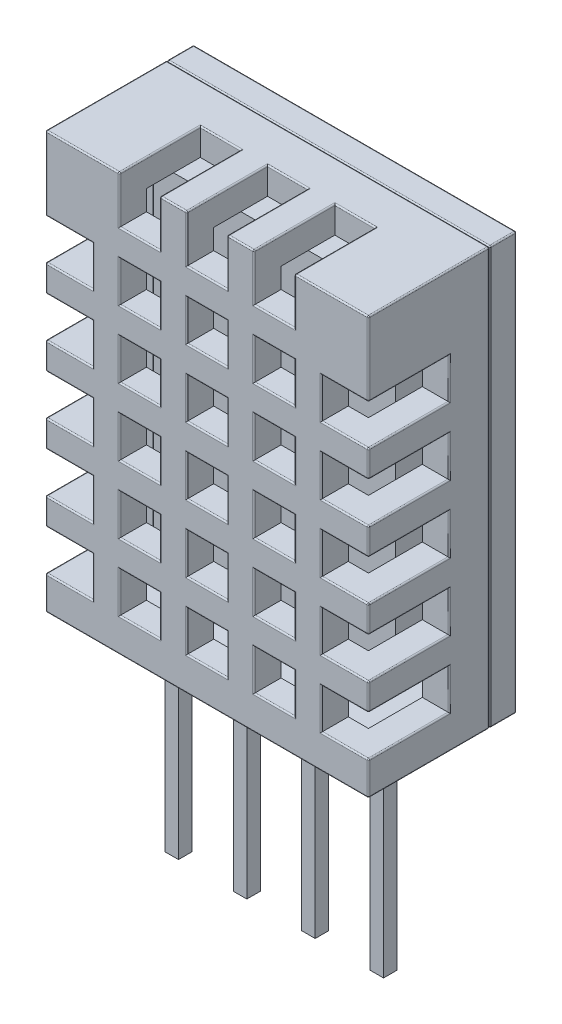
SolidWorks part; units mm, degrees
ref_plane "Front Plane" through (0, 0, 0) normal (0, 0, 1) x (1, 0, 0)
ref_plane "Top Plane" through (0, 0, 0) normal (0, 1, 0) x (1, 0, 0)
ref_plane "Right Plane" through (0, 0, 0) normal (1, 0, 0) x (0, 0, -1)
sketch "Sketch1" plane through (0, 0, 0) normal (0, 0, 1) x (1, 0, 0)
  line L1 (0, 0) -> (12, 0)
  line L2 (0, 0) -> (0, 15.5)
  line L3 (0, 15.5) -> (12, 15.5)
  line L4 (12, 0) -> (12, 15.5)
  dimension "D1" = 12
  dimension "D2" = 15.5
extrude "Boss-Extrude1" add sketch "Sketch1" along normal blind 5.5
sketch "Sketch2" plane through (0, 0, 0) normal (0, -1, 0) x (1, 0, 0)
  line L0 (0, 5.5) -> (0, 0) construction
  line L1 (1.94, 3) -> (2.44, 3)
  line L2 (1.94, 3) -> (1.94, 2.5)
  line L3 (1.94, 2.5) -> (2.44, 2.5)
  line L4 (2.44, 3) -> (2.44, 2.5)
  line L5 (0, 2.75) -> (12, 2.75) construction
  line L6 (12, 5.5) -> (12, 0) construction
  line L7 (4.48, 3) -> (4.98, 3)
  line L8 (4.48, 3) -> (4.48, 2.5)
  line L9 (4.48, 2.5) -> (4.98, 2.5)
  line L10 (4.98, 3) -> (4.98, 2.5)
  line L11 (7.02, 3) -> (7.52, 3)
  line L12 (7.02, 3) -> (7.02, 2.5)
  line L13 (7.02, 2.5) -> (7.52, 2.5)
  line L14 (7.52, 3) -> (7.52, 2.5)
  line L15 (9.56, 3) -> (10.06, 3)
  line L16 (9.56, 3) -> (9.56, 2.5)
  line L17 (9.56, 2.5) -> (10.06, 2.5)
  line L18 (10.06, 3) -> (10.06, 2.5)
  point P11 (1.94, 2.75)
  dimension "D1" = 0.5
  dimension "D2" = 0.5
  dimension "D3" = 1.94
  dimension "D4" = 4
extrude "Boss-Extrude2" add sketch "Sketch2" along normal blind 8
shell "Shell2" thickness 1
sketch "Sketch3" plane through (0, 0, 5.5) normal (0, 0, 1) x (1, 0, 0)
  line L0 (12, 15.5) -> (0, 15.5) construction
  line L1 (2.75, 15.5) -> (4.25, 15.5)
  line L2 (2.75, 15.5) -> (2.75, 13.75)
  line L3 (2.75, 13.75) -> (4.25, 13.75)
  line L4 (4.25, 15.5) -> (4.25, 13.75)
  line L5 (5.25, 15.5) -> (6.75, 15.5)
  line L6 (5.25, 15.5) -> (5.25, 13.75)
  line L7 (5.25, 13.75) -> (6.75, 13.75)
  line L8 (6.75, 15.5) -> (6.75, 13.75)
  line L9 (7.75, 15.5) -> (9.25, 15.5)
  line L10 (7.75, 15.5) -> (7.75, 13.75)
  line L11 (7.75, 13.75) -> (9.25, 13.75)
  line L12 (9.25, 15.5) -> (9.25, 13.75)
  line L13 (0, 15.5) -> (0, 0) construction
  dimension "D1" = 1.5
  dimension "D2" = 1.75
  dimension "D4" = 2.75
  dimension "D3" = 3
extrude "Cut-Extrude1" cut sketch "Sketch3" against normal blind 3
sketch "Sketch4" plane through (0, 0, 5.5) normal (0, 0, 1) x (1, 0, 0)
  line L0 (2.75, 13.75) -> (4.25, 13.75) construction
  line L1 (2.75, 12.75) -> (4.25, 12.75)
  line L2 (2.75, 12.75) -> (2.75, 11.25)
  line L3 (2.75, 11.25) -> (4.25, 11.25)
  line L4 (4.25, 12.75) -> (4.25, 11.25)
  line L5 (0, 15.5) -> (0, 0) construction
  line L6 (5.25, 12.75) -> (6.75, 12.75)
  line L7 (5.25, 12.75) -> (5.25, 11.25)
  line L8 (5.25, 11.25) -> (6.75, 11.25)
  line L9 (6.75, 12.75) -> (6.75, 11.25)
  line L10 (7.75, 12.75) -> (9.25, 12.75)
  line L11 (7.75, 12.75) -> (7.75, 11.25)
  line L12 (7.75, 11.25) -> (9.25, 11.25)
  line L13 (9.25, 12.75) -> (9.25, 11.25)
  line L14 (5.25, 10.25) -> (6.75, 10.25)
  line L15 (5.25, 10.25) -> (5.25, 8.75)
  line L16 (5.25, 8.75) -> (6.75, 8.75)
  line L17 (6.75, 10.25) -> (6.75, 8.75)
  line L18 (7.75, 10.25) -> (9.25, 10.25)
  line L19 (7.75, 10.25) -> (7.75, 8.75)
  line L20 (7.75, 8.75) -> (9.25, 8.75)
  line L21 (9.25, 10.25) -> (9.25, 8.75)
  line L22 (5.25, 7.75) -> (6.75, 7.75)
  line L23 (5.25, 7.75) -> (5.25, 6.25)
  line L24 (5.25, 6.25) -> (6.75, 6.25)
  line L25 (6.75, 7.75) -> (6.75, 6.25)
  line L26 (7.75, 7.75) -> (9.25, 7.75)
  line L27 (7.75, 7.75) -> (7.75, 6.25)
  line L28 (7.75, 6.25) -> (9.25, 6.25)
  line L29 (9.25, 7.75) -> (9.25, 6.25)
  line L30 (5.25, 5.25) -> (6.75, 5.25)
  line L31 (5.25, 5.25) -> (5.25, 3.75)
  line L32 (5.25, 3.75) -> (6.75, 3.75)
  line L33 (6.75, 5.25) -> (6.75, 3.75)
  line L34 (7.75, 5.25) -> (9.25, 5.25)
  line L35 (7.75, 5.25) -> (7.75, 3.75)
  line L36 (7.75, 3.75) -> (9.25, 3.75)
  line L37 (9.25, 5.25) -> (9.25, 3.75)
  line L38 (5.25, 2.75) -> (6.75, 2.75)
  line L39 (5.25, 2.75) -> (5.25, 1.25)
  line L40 (5.25, 1.25) -> (6.75, 1.25)
  line L41 (6.75, 2.75) -> (6.75, 1.25)
  line L42 (7.75, 2.75) -> (9.25, 2.75)
  line L43 (7.75, 2.75) -> (7.75, 1.25)
  line L44 (7.75, 1.25) -> (9.25, 1.25)
  line L45 (9.25, 2.75) -> (9.25, 1.25)
  line L46 (2.75, 10.25) -> (4.25, 10.25)
  line L47 (2.75, 10.25) -> (2.75, 8.75)
  line L48 (2.75, 8.75) -> (4.25, 8.75)
  line L49 (4.25, 10.25) -> (4.25, 8.75)
  line L50 (2.75, 7.75) -> (4.25, 7.75)
  line L51 (2.75, 7.75) -> (2.75, 6.25)
  line L52 (2.75, 6.25) -> (4.25, 6.25)
  line L53 (4.25, 7.75) -> (4.25, 6.25)
  line L54 (2.75, 5.25) -> (4.25, 5.25)
  line L55 (2.75, 5.25) -> (2.75, 3.75)
  line L56 (2.75, 3.75) -> (4.25, 3.75)
  line L57 (4.25, 5.25) -> (4.25, 3.75)
  line L58 (2.75, 2.75) -> (4.25, 2.75)
  line L59 (2.75, 2.75) -> (2.75, 1.25)
  line L60 (2.75, 1.25) -> (4.25, 1.25)
  line L61 (4.25, 2.75) -> (4.25, 1.25)
  dimension "D1" = 1.5
  dimension "D2" = 1
  dimension "D3" = 2.75
  dimension "D4" = 3
  dimension "D5" = 5
extrude "Cut-Extrude2" cut sketch "Sketch4" against normal blind 3
sketch "Sketch5" plane through (0, 0, 5.5) normal (0, 0, 1) x (1, 0, 0)
  line L0 (0, 15.5) -> (0, 0) construction
  line L1 (0, 12.75) -> (1.75, 12.75)
  line L2 (0, 12.75) -> (0, 11.25)
  line L3 (0, 11.25) -> (1.75, 11.25)
  line L4 (1.75, 12.75) -> (1.75, 11.25)
  line L7 (2.75, 12.75) -> (2.75, 11.25) construction
  line L8 (10.25, 12.75) -> (12, 12.75)
  line L9 (10.25, 12.75) -> (10.25, 11.25)
  line L10 (10.25, 11.25) -> (12, 11.25)
  line L11 (12, 12.75) -> (12, 11.25)
  line L12 (10.25, 10.25) -> (12, 10.25)
  line L13 (10.25, 10.25) -> (10.25, 8.75)
  line L14 (10.25, 8.75) -> (12, 8.75)
  line L15 (12, 10.25) -> (12, 8.75)
  line L16 (10.25, 7.75) -> (12, 7.75)
  line L17 (10.25, 7.75) -> (10.25, 6.25)
  line L18 (10.25, 6.25) -> (12, 6.25)
  line L19 (12, 7.75) -> (12, 6.25)
  line L20 (10.25, 5.25) -> (12, 5.25)
  line L21 (10.25, 5.25) -> (10.25, 3.75)
  line L22 (10.25, 3.75) -> (12, 3.75)
  line L23 (12, 5.25) -> (12, 3.75)
  line L24 (10.25, 2.75) -> (12, 2.75)
  line L25 (10.25, 2.75) -> (10.25, 1.25)
  line L26 (10.25, 1.25) -> (12, 1.25)
  line L27 (12, 2.75) -> (12, 1.25)
  line L28 (0, 10.25) -> (1.75, 10.25)
  line L29 (0, 10.25) -> (0, 8.75)
  line L30 (0, 8.75) -> (1.75, 8.75)
  line L31 (1.75, 10.25) -> (1.75, 8.75)
  line L32 (0, 7.75) -> (1.75, 7.75)
  line L33 (0, 7.75) -> (0, 6.25)
  line L34 (0, 6.25) -> (1.75, 6.25)
  line L35 (1.75, 7.75) -> (1.75, 6.25)
  line L36 (0, 5.25) -> (1.75, 5.25)
  line L37 (0, 5.25) -> (0, 3.75)
  line L38 (0, 3.75) -> (1.75, 3.75)
  line L39 (1.75, 5.25) -> (1.75, 3.75)
  line L40 (0, 2.75) -> (1.75, 2.75)
  line L41 (0, 2.75) -> (0, 1.25)
  line L42 (0, 1.25) -> (1.75, 1.25)
  line L43 (1.75, 2.75) -> (1.75, 1.25)
  dimension "D1" = 1
  dimension "D2" = 2
  dimension "D3" = 5
extrude "Cut-Extrude3" cut sketch "Sketch5" against normal blind 3
sketch "Sketch6" plane through (0, 0, 0) normal (0, 0, -1) x (-1, 0, 0)
  line L4 (0, 0) -> (0, 15.5)
  line L5 (0, 15.5) -> (-12, 15.5)
  line L6 (-12, 15.5) -> (-12, 0)
  line L7 (-12, 0) -> (0, 0)
  line L8 (0, 0) -> (0, 15.5)
  line L9 (0, 15.5) -> (-12, 15.5)
  line L10 (-12, 15.5) -> (-12, 0)
  line L11 (-12, 0) -> (0, 0)
  line L12 (-1, 14.5) -> (-11, 14.5)
  line L13 (-1, 1) -> (-1, 14.5)
  line L14 (-11, 1) -> (-1, 1)
  line L15 (-11, 14.5) -> (-11, 1)
  line L16 (-1, 14.5) -> (-11, 14.5)
  line L17 (-1, 1) -> (-1, 14.5)
  line L18 (-11, 1) -> (-1, 1)
  line L19 (-11, 14.5) -> (-11, 1)
  dimension "D1" = 0
  dimension "D2" = 0
extrude "Cut-Extrude4" cut sketch "Sketch6" against normal blind 1
ref_plane "Plane1" through (0, 0, 0.99) normal (0, 0, 1) x (1, 0, 0)
sketch "Sketch8" plane through (0, 0, 0.99) normal (0, 0, 1) x (1, 0, 0)
  line L4 (0, 0) -> (12, 0)
  line L5 (0, 15.5) -> (0, 0)
  line L6 (12, 15.5) -> (0, 15.5)
  line L7 (12, 0) -> (12, 15.5)
  line L8 (0, 0) -> (12, 0)
  line L9 (0, 15.5) -> (0, 0)
  line L10 (12, 15.5) -> (0, 15.5)
  line L11 (12, 0) -> (12, 15.5)
  dimension "D1" = 0
extrude "Boss-Extrude3" add sketch "Sketch8" against normal blind 0.99 separate body
sketch "Sketch9" plane through (0, 0, 0) normal (0, -1, 0) x (1, 0, 0)
  line L0 (1.94, 3) -> (1.94, 2.5) construction
  line L1 (1.94, 2.5) -> (2.44, 2.5) construction
  line L2 (2.44, 2.5) -> (2.44, 3) construction
  line L3 (2.44, 3) -> (1.94, 3) construction
  line L4 (4.48, 3) -> (4.48, 2.5) construction
  line L5 (4.48, 2.5) -> (4.98, 2.5) construction
  line L6 (4.98, 2.5) -> (4.98, 3) construction
  line L7 (4.98, 3) -> (4.48, 3) construction
  line L8 (7.02, 3) -> (7.02, 2.5) construction
  line L9 (7.02, 2.5) -> (7.52, 2.5) construction
  line L10 (7.52, 2.5) -> (7.52, 3) construction
  line L11 (7.52, 3) -> (7.02, 3) construction
  line L12 (9.56, 3) -> (9.56, 2.5) construction
  line L13 (9.56, 2.5) -> (10.06, 2.5) construction
  line L14 (10.06, 2.5) -> (10.06, 3) construction
  line L15 (10.06, 3) -> (9.56, 3) construction
  line L16 (1.94, 3) -> (1.94, 2.5)
  line L17 (1.94, 2.5) -> (2.44, 2.5)
  line L18 (2.44, 2.5) -> (2.44, 3)
  line L19 (2.44, 3) -> (1.94, 3)
  line L20 (4.48, 3) -> (4.48, 2.5)
  line L21 (4.48, 2.5) -> (4.98, 2.5)
  line L22 (4.98, 2.5) -> (4.98, 3)
  line L23 (4.98, 3) -> (4.48, 3)
  line L24 (7.02, 3) -> (7.02, 2.5)
  line L25 (7.02, 2.5) -> (7.52, 2.5)
  line L26 (7.52, 2.5) -> (7.52, 3)
  line L27 (7.52, 3) -> (7.02, 3)
  line L28 (9.56, 3) -> (9.56, 2.5)
  line L29 (9.56, 2.5) -> (10.06, 2.5)
  line L30 (10.06, 2.5) -> (10.06, 3)
  line L31 (10.06, 3) -> (9.56, 3)
  line L32 (1.84, 3.1) -> (1.84, 2.4)
  line L33 (1.84, 2.4) -> (2.54, 2.4)
  line L34 (2.54, 2.4) -> (2.54, 3.1)
  line L35 (2.54, 3.1) -> (1.84, 3.1)
  line L36 (4.38, 3.1) -> (4.38, 2.4)
  line L37 (4.38, 2.4) -> (5.08, 2.4)
  line L38 (5.08, 2.4) -> (5.08, 3.1)
  line L39 (5.08, 3.1) -> (4.38, 3.1)
  line L40 (6.92, 3.1) -> (6.92, 2.4)
  line L41 (6.92, 2.4) -> (7.62, 2.4)
  line L42 (7.62, 2.4) -> (7.62, 3.1)
  line L43 (7.62, 3.1) -> (6.92, 3.1)
  line L44 (9.46, 3.1) -> (9.46, 2.4)
  line L45 (9.46, 2.4) -> (10.16, 2.4)
  line L46 (10.16, 2.4) -> (10.16, 3.1)
  line L47 (10.16, 3.1) -> (9.46, 3.1)
  dimension "D1" = 0.1
extrude "Cut-Extrude5" cut sketch "Sketch9" against normal blind 1
fillet "Fillet1" radius 0.05 106 edges at (2.19, 0, 2.4) (2.54, 0, 2.75) (1.84, 0, 2.75) (4.73, 0, 2.4) (4.38, 0, 2.75) (7.62, 0, 2.75) (7.27, 0, 3.1) (10.16, 0, 2.75) (0, 12.75, 4) (0, 12, 2.5) (0, 11.25, 4) (0, 10.25, 4) (0, 8.75, 4) (0, 6.25, 4) (0, 4.5, 2.5) (0, 3.75, 4) (0, 2.75, 4) (0, 2, 2.5) (0, 1.25, 4) (0, 0, 3.25) (0, 7.75, 1) (9.25, 15.5, 4) (7.75, 15.5, 4) (5.25, 15.5, 4) (4.25, 15.5, 4) (2.75, 15.5, 4) (0, 15.5, 3.25) (12, 0, 3.25) (12, 2, 2.5) (12, 2.75, 4) (12, 3.75, 4) (12, 4.5, 2.5) (12, 5.25, 4) (12, 7.75, 4) (12, 8.75, 4) (12, 9.5, 2.5) (12, 10.25, 4) (12, 15.5, 3.25) (12, 7.75, 1) (1.75, 4.5, 5.5) (0.875, 5.25, 5.5) (0, 5.75, 5.5) (0.875, 6.25, 5.5) (1.75, 7, 5.5) (0, 8.25, 5.5) (0.875, 8.75, 5.5) (1.75, 9.5, 5.5) (1.75, 12, 5.5) (0.875, 12.75, 5.5) (0, 14.125, 5.5) (1.375, 15.5, 5.5) (4.25, 14.625, 5.5) (7.75, 14.625, 5.5) (10.625, 15.5, 5.5) (12, 14.125, 5.5) (11.125, 11.25, 5.5) (12, 10.75, 5.5) (10.25, 9.5, 5.5) (11.125, 8.75, 5.5) (11.125, 6.25, 5.5) (12, 5.75, 5.5) (11.125, 3.75, 5.5) (12, 3.25, 5.5) (11.125, 2.75, 5.5) (12, 0.625, 5.5) (0.875, 1.25, 5.5) (1.75, 2, 5.5) (0.875, 2.75, 5.5) (4.25, 12, 5.5) (2.75, 12, 5.5) (6.75, 12, 5.5) (6, 12.75, 5.5) (5.25, 12, 5.5) (6, 11.25, 5.5) (9.25, 12, 5.5) (8.5, 12.75, 5.5) (6.75, 9.5, 5.5) (6, 10.25, 5.5) (6, 8.75, 5.5) (9.25, 9.5, 5.5) (8.5, 10.25, 5.5) (8.5, 8.75, 5.5) (6, 7.75, 5.5) (6, 6.25, 5.5) (9.25, 7, 5.5) (8.5, 7.75, 5.5) (8.5, 6.25, 5.5) (6, 5.25, 5.5) (5.25, 4.5, 5.5) (9.25, 4.5, 5.5) (7.75, 4.5, 5.5) (8.5, 3.75, 5.5) (6.75, 2, 5.5) (6, 2.75, 5.5) (5.25, 2, 5.5) (6, 1.25, 5.5) (9.25, 2, 5.5) (7.75, 2, 5.5) (3.5, 10.25, 5.5) (2.75, 9.5, 5.5) (3.5, 7.75, 5.5) (2.75, 7, 5.5) (3.5, 6.25, 5.5) (2.75, 4.5, 5.5) (2.75, 2, 5.5) (3.5, 1.25, 5.5)
fillet "Fillet2" radius 0.05 12 edges at (6, 15.5, 0.99) (0, 15.5, 0.495) (0, 7.75, 0.99) (0, 0, 0.495) (6, 0, 0.99) (12, 15.5, 0.495) (12, 0, 0.495) (12, 7.75, 0.99) (6, 15.5, 0) (0, 7.75, 0) (6, 0, 0) (12, 7.75, 0)
sketch "Sketch10" plane through (0, 0, 0.99) normal (0, 0, 1) x (1, 0, 0)
  line L14 (1.5, 1.5) -> (10.5, 1.5)
  line L15 (10.5, 1.5) -> (10.5, 14)
  line L16 (10.5, 14) -> (1.5, 14)
  line L17 (1.5, 14) -> (1.5, 1.5)
  line L18 (1.5, 1.5) -> (10.5, 1.5)
  line L19 (10.5, 1.5) -> (10.5, 14)
  line L20 (10.5, 14) -> (1.5, 14)
  line L21 (1.5, 14) -> (1.5, 1.5)
  dimension "D1" = 0.5
extrude "Boss-Extrude4" add sketch "Sketch10" along normal blind 2
